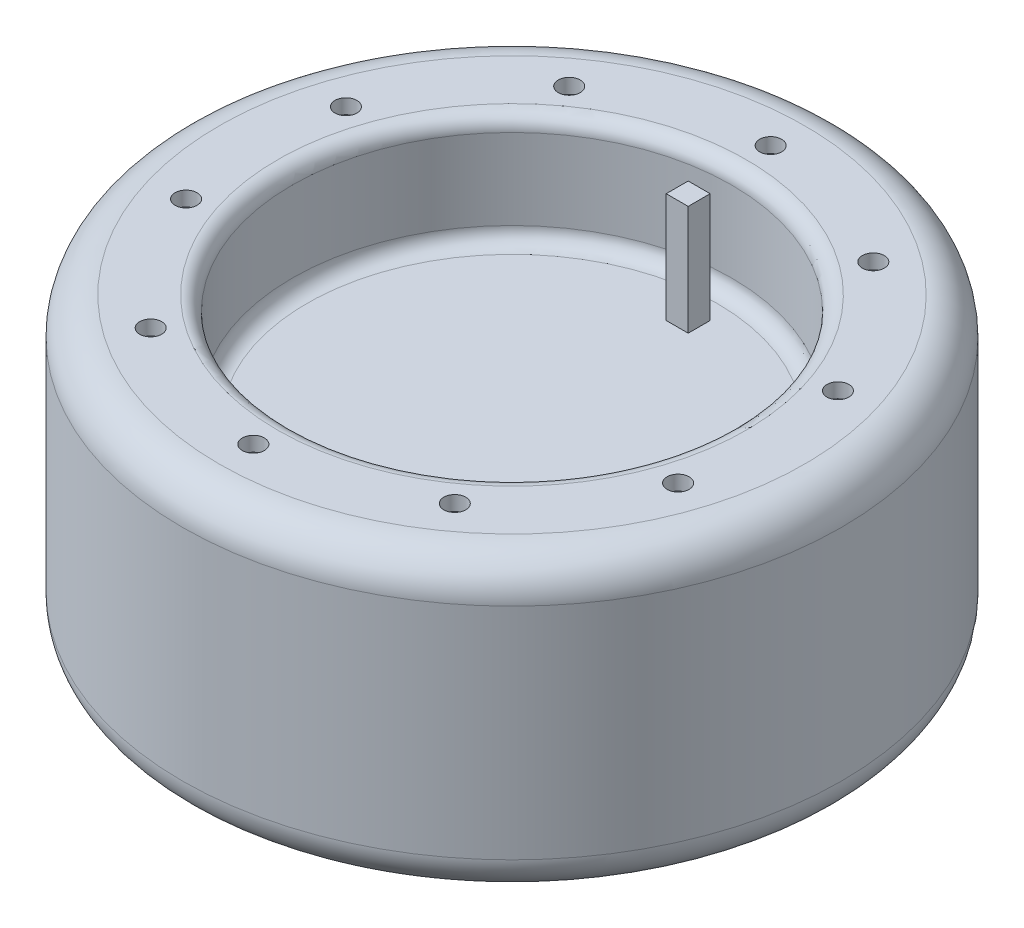
SolidWorks part; units mm, degrees
ref_plane "Front Plane" through (0, 0, 0) normal (0, 0, 1) x (1, 0, 0)
ref_plane "Top Plane" through (0, 0, 0) normal (0, 1, 0) x (1, 0, 0)
ref_plane "Right Plane" through (0, 0, 0) normal (1, 0, 0) x (0, 0, -1)
sketch "Sketch1" plane through (0, 0, 0) normal (0, 1, 0) x (1, 0, 0)
  circle A0 centre (0, 0) radius 45
  dimension "D1" = 90
extrude "Boss-Extrude1" add sketch "Sketch1" along normal blind 40
fillet "Fillet1" radius 5 2 edges at (0, 40, 45) (0, 0, 45)
sketch "Sketch2" plane through (0, 40, 0) normal (0, 1, 0) x (1, 0, 0)
  circle A0 centre (0, 0) radius 30
extrude "Cut-Extrude1" cut sketch "Sketch2" against normal blind 15
fillet "Fillet2" radius 2 2 edges at (0, 40, 30) (0, 25, 30)
sketch "Sketch3" plane through (0, 40, 0) normal (0, 1, 0) x (1, 0, 0)
  circle A0 centre (0, 35.324) radius 1.5
  circle A1 centre (20.7629, 28.5777) radius 1.5
  circle A2 centre (33.5951, 10.9157) radius 1.5
  circle A3 centre (33.5951, -10.9157) radius 1.5
  circle A4 centre (20.7629, -28.5777) radius 1.5
  circle A5 centre (0, -35.324) radius 1.5
  circle A6 centre (-20.7629, -28.5777) radius 1.5
  circle A7 centre (-33.5951, -10.9157) radius 1.5
  circle A8 centre (-33.5951, 10.9157) radius 1.5
  circle A9 centre (-20.7629, 28.5777) radius 1.5
  point P23 (0, 0)
  dimension "D1" = 10
extrude "Cut-Extrude2" cut sketch "Sketch3" against normal blind 2
sketch "Sketch4" plane through (0, 25, 0) normal (0, 1, 0) x (1, 0, 0)
  line L1 (-1.4407, 25.5) -> (1.5593, 25.5)
  line L2 (-1.4407, 25.5) -> (-1.4407, 22.5)
  line L3 (-1.4407, 22.5) -> (1.5593, 22.5)
  line L4 (1.5593, 25.5) -> (1.5593, 22.5)
  line L5 (-1.4407, 25.5) -> (1.5593, 22.5) construction
  line L6 (-1.4407, 22.5) -> (1.5593, 25.5) construction
  point P0 (0.0593, 24)
  dimension "D1" = 3
  dimension "D2" = 3
  dimension "D3" = 24
extrude "Boss-Extrude2" add sketch "Sketch4" along normal up to surface (15 mm away) up to face at (0, 40, -33.824)
